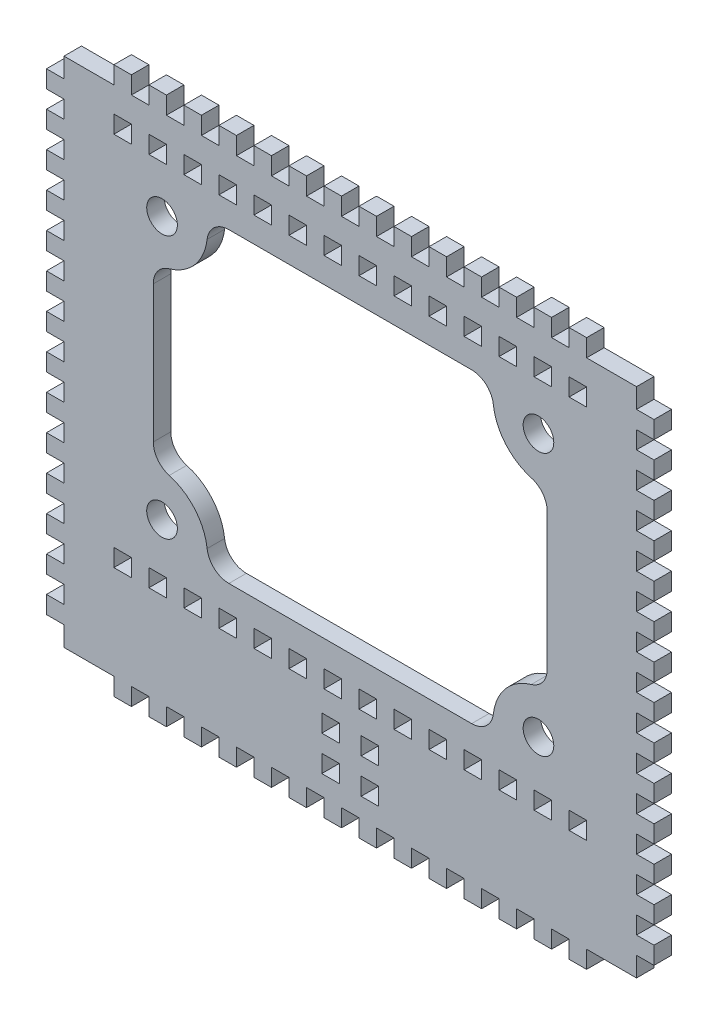
SolidWorks part; units mm, degrees
material "Cedar"
ref_plane "Front Plane" through (0, 0, 0) normal (0, 0, 1) x (1, 0, 0)
ref_plane "Top Plane" through (0, 0, 0) normal (0, 1, 0) x (1, 0, 0)
ref_plane "Right Plane" through (0, 0, 0) normal (1, 0, 0) x (0, 0, -1)
sketch "Sketch1" plane through (0, 0, 0) normal (0, 0, 1) x (1, 0, 0)
  line L0 (0, 0) -> (0, 50) construction
  line L1 (0, 0) -> (-64, 0) construction
  line L2 (-65.4, -66.5) -> (-65.4, -62)
  line L3 (-65.4, 50.5) -> (65.4, 50.5)
  line L4 (-45, -20) -> (-45, 20)
  line L5 (-33, 35) -> (33, 35)
  line L6 (45, -20) -> (45, 20)
  line L7 (65.4, -66.5) -> (65.4, -62)
  line L8 (-65.4, -66.5) -> (65.4, -66.5)
  line L9 (-33, -35) -> (33, -35)
  line L10 (-54.7956, 50.5) -> (-54.7956, -66.5) construction
  line L11 (-65.4, -2) -> (-69.4, -2)
  line L12 (-65.4, -2) -> (-65.4, 2)
  line L13 (-65.4, -6) -> (-69.4, -6)
  line L14 (-69.4, -2) -> (-69.4, -6)
  line L15 (-54.7956, -8) -> (-65.4, -8) construction
  line L16 (-65.4, 6) -> (-69.4, 6)
  line L17 (65.4, -58) -> (65.4, -54)
  line L18 (-65.4, 2) -> (-69.4, 2)
  line L19 (-69.4, 6) -> (-69.4, 2)
  line L20 (-65.4, 14) -> (-69.4, 14)
  line L21 (-65.4, -58) -> (-65.4, -54)
  line L22 (-65.4, 10) -> (-69.4, 10)
  line L23 (-69.4, 14) -> (-69.4, 10)
  line L24 (-65.4, 22) -> (-69.4, 22)
  line L25 (-65.4, 14) -> (-65.4, 18)
  line L26 (-65.4, 18) -> (-69.4, 18)
  line L27 (-69.4, 22) -> (-69.4, 18)
  line L28 (-65.4, 30) -> (-69.4, 30)
  line L29 (-65.4, 22) -> (-65.4, 26)
  line L30 (-65.4, 26) -> (-69.4, 26)
  line L31 (-69.4, 30) -> (-69.4, 26)
  line L32 (-65.4, 38) -> (-69.4, 38)
  line L33 (-65.4, 46) -> (-65.4, 50.5)
  line L34 (-65.4, 34) -> (-69.4, 34)
  line L35 (-69.4, 38) -> (-69.4, 34)
  line L36 (-65.4, 46) -> (-69.4, 46)
  line L37 (-65.4, 30) -> (-65.4, 34)
  line L38 (-65.4, 42) -> (-69.4, 42)
  line L39 (-69.4, 46) -> (-69.4, 42)
  line L40 (-69.4, -62) -> (-69.4, -58)
  line L41 (-65.4, -58) -> (-69.4, -58)
  line L42 (-65.4, -50) -> (-65.4, -46)
  line L43 (-65.4, -62) -> (-69.4, -62)
  line L44 (-69.4, -54) -> (-69.4, -50)
  line L45 (-65.4, -50) -> (-69.4, -50)
  line L46 (-65.4, -42) -> (-65.4, -38)
  line L47 (-65.4, -54) -> (-69.4, -54)
  line L48 (-69.4, -46) -> (-69.4, -42)
  line L49 (-65.4, -42) -> (-69.4, -42)
  line L50 (-65.4, -34) -> (-65.4, -30)
  line L51 (-65.4, -46) -> (-69.4, -46)
  line L52 (-69.4, -38) -> (-69.4, -34)
  line L53 (-65.4, -34) -> (-69.4, -34)
  line L55 (-65.4, -38) -> (-69.4, -38)
  line L56 (-69.4, -30) -> (-69.4, -26)
  line L57 (-65.4, -26) -> (-69.4, -26)
  line L58 (-65.4, -18) -> (-65.4, -14)
  line L59 (-65.4, -30) -> (-69.4, -30)
  line L60 (-69.4, -22) -> (-69.4, -18)
  line L61 (-65.4, -18) -> (-69.4, -18)
  line L62 (-65.4, -10) -> (-65.4, -6)
  line L63 (-65.4, -22) -> (-69.4, -22)
  line L64 (-69.4, -14) -> (-69.4, -10)
  line L65 (-65.4, -10) -> (-69.4, -10)
  line L66 (-65.4, 6) -> (-65.4, 10)
  line L67 (-65.4, -14) -> (-69.4, -14)
  line L68 (65.4, -14) -> (69.4, -14)
  line L69 (65.4, -10) -> (65.4, -6)
  line L70 (65.4, -10) -> (69.4, -10)
  line L71 (69.4, -14) -> (69.4, -10)
  line L72 (65.4, -22) -> (69.4, -22)
  line L73 (65.4, -18) -> (65.4, -14)
  line L74 (65.4, -18) -> (69.4, -18)
  line L75 (69.4, -22) -> (69.4, -18)
  line L76 (65.4, -30) -> (69.4, -30)
  line L77 (65.4, -26) -> (65.4, -22)
  line L78 (65.4, -26) -> (69.4, -26)
  line L79 (69.4, -30) -> (69.4, -26)
  line L80 (65.4, -38) -> (69.4, -38)
  line L81 (65.4, -34) -> (65.4, -30)
  line L82 (65.4, -34) -> (69.4, -34)
  line L83 (69.4, -38) -> (69.4, -34)
  line L84 (65.4, -46) -> (69.4, -46)
  line L85 (65.4, -50) -> (65.4, -46)
  line L86 (65.4, -42) -> (69.4, -42)
  line L87 (69.4, -46) -> (69.4, -42)
  line L88 (65.4, -54) -> (69.4, -54)
  line L89 (65.4, -2) -> (65.4, 2)
  line L90 (65.4, -50) -> (69.4, -50)
  line L91 (69.4, -54) -> (69.4, -50)
  line L92 (65.4, -62) -> (69.4, -62)
  line L93 (65.4, -42) -> (65.4, -38)
  line L94 (65.4, -58) -> (69.4, -58)
  line L95 (69.4, -62) -> (69.4, -58)
  line L96 (69.4, 46) -> (69.4, 42)
  line L97 (65.4, 42) -> (69.4, 42)
  line L98 (65.4, 46) -> (65.4, 50.5)
  line L99 (65.4, 46) -> (69.4, 46)
  line L100 (69.4, 38) -> (69.4, 34)
  line L101 (65.4, 34) -> (69.4, 34)
  line L102 (65.4, 38) -> (65.4, 42)
  line L103 (65.4, 38) -> (69.4, 38)
  line L104 (69.4, 30) -> (69.4, 26)
  line L105 (65.4, 26) -> (69.4, 26)
  line L106 (65.4, 30) -> (65.4, 34)
  line L107 (65.4, 30) -> (69.4, 30)
  line L108 (69.4, 22) -> (69.4, 18)
  line L109 (65.4, 18) -> (69.4, 18)
  line L110 (65.4, 22) -> (65.4, 26)
  line L111 (65.4, 22) -> (69.4, 22)
  line L112 (69.4, 14) -> (69.4, 10)
  line L113 (65.4, 10) -> (69.4, 10)
  line L114 (65.4, 14) -> (65.4, 18)
  line L115 (65.4, 14) -> (69.4, 14)
  line L116 (69.4, 6) -> (69.4, 2)
  line L117 (65.4, 2) -> (69.4, 2)
  line L119 (65.4, 6) -> (69.4, 6)
  line L120 (69.4, -2) -> (69.4, -6)
  line L121 (65.4, -6) -> (69.4, -6)
  line L123 (65.4, -2) -> (69.4, -2)
  line L124 (-65.4, 38) -> (-65.4, 42)
  line L130 (-65.4, -26) -> (-65.4, -22)
  line L131 (65.4, 6) -> (65.4, 10)
  circle A0 centre (-43, 30) radius 3.5
  arc A1 (-45, 20) -> (-33, 35) centre (-44.6174, 31.9939) ccw
  arc A2 (45, -20) -> (33, -35) centre (44.6174, -31.9939) ccw
  circle A3 centre (43, 30) radius 3.5
  circle A4 centre (43, -30) radius 3.5
  circle A5 centre (-43, -30) radius 3.5
  arc A6 (45, 20) -> (33, 35) centre (44.6174, 31.9939) cw
  arc A7 (-45, -20) -> (-33, -35) centre (-44.6174, -31.9939) cw
  point P19 (0, 35)
  point P21 (0, 50.5)
  point P27 (-64, 0)
  point P28 (64, 0)
  point P29 (45, 0)
  point P34 (-45, 0)
  point P94 (-64, -16)
  point P151 (64, -16)
  dimension "D3" = 7
  dimension "D8" = 50.5
  dimension "D7" = 10
  dimension "D9" = 35
  dimension "D10" = 12
  dimension "D11" = 66.5
  dimension "D1" = 10
  dimension "D2" = 130.8
  dimension "D4" = 43
  dimension "D5" = 45
  dimension "D6" = 30
  dimension "D12" = 4
  dimension "D13" = 2
  dimension "D14" = 4
  dimension "D15" = 7
extrude "Boss-Extrude1" add sketch "Sketch1" along normal blind 4
sketch "Sketch3" plane through (0, 0, 4) normal (0, 0, 1) x (1, 0, 0)
  line L0 (0, 0) -> (0, 54.6046) construction
  line L2 (-54, -45) -> (-50, -45)
  line L3 (-54, -45) -> (-54, -41)
  line L4 (-54, -41) -> (-50, -41)
  line L5 (-50, -45) -> (-50, -41)
  line L6 (33, 35) -> (33, 50.5) construction
  line L7 (-65.4, 50.5) -> (65.4, 50.5) construction
  line L8 (42, -45) -> (42, -41)
  line L9 (46, -41) -> (42, -41)
  line L10 (46, -45) -> (46, -41)
  line L11 (-6.5, -50) -> (-2.5, -50)
  line L12 (46, -45) -> (42, -45)
  line L13 (0, -35) -> (0, -66.5) construction
  line L14 (34, -45) -> (34, -41)
  line L15 (0, 0) -> (-26.3378, 0) construction
  line L16 (0, 0) -> (-64, 0) construction
  line L17 (-33, -35) -> (33, -35) construction
  line L18 (-65.4, -66.5) -> (65.4, -66.5) construction
  line L19 (38, -41) -> (34, -41)
  line L20 (38, -45) -> (38, -41)
  line L21 (38, -45) -> (34, -45)
  line L22 (26, -45) -> (26, -41)
  line L23 (30, -41) -> (26, -41)
  line L24 (30, -45) -> (30, -41)
  line L25 (30, -45) -> (26, -45)
  line L26 (18, -45) -> (18, -41)
  line L27 (22, -41) -> (18, -41)
  line L28 (22, -45) -> (22, -41)
  line L29 (22, -45) -> (18, -45)
  line L30 (10, -45) -> (10, -41)
  line L31 (14, -41) -> (10, -41)
  line L32 (14, -45) -> (14, -41)
  line L33 (2, -45) -> (2, -41)
  line L34 (-6.5, -50) -> (-6.5, -54)
  line L35 (6, -41) -> (2, -41)
  line L36 (6, -45) -> (6, -41)
  line L37 (6, -45) -> (2, -45)
  line L38 (-6.5, -54) -> (-2.5, -54)
  line L39 (14, -45) -> (10, -45)
  line L40 (50, -45) -> (50, -41)
  line L41 (54, -41) -> (50, -41)
  line L42 (54, -45) -> (54, -41)
  line L43 (54, -45) -> (50, -45)
  line L44 (33, 42.75) -> (-16.2732, 42.75) construction
  line L45 (-14, 40.75) -> (-10, 40.75)
  line L46 (-6, 40.75) -> (-2, 40.75)
  line L47 (-6, 40.75) -> (-6, 44.75)
  line L48 (-6, 44.75) -> (-2, 44.75)
  line L49 (-2, 40.75) -> (-2, 44.75)
  line L50 (-14, 40.75) -> (-14, 44.75)
  line L51 (-14, 44.75) -> (-10, 44.75)
  line L52 (-10, 40.75) -> (-10, 44.75)
  line L53 (-22, 40.75) -> (-18, 40.75)
  line L54 (-22, 40.75) -> (-22, 44.75)
  line L55 (-22, 44.75) -> (-18, 44.75)
  line L56 (-18, 40.75) -> (-18, 44.75)
  line L57 (-30, 40.75) -> (-26, 40.75)
  line L58 (-30, 40.75) -> (-30, 44.75)
  line L59 (-30, 44.75) -> (-26, 44.75)
  line L60 (-26, 40.75) -> (-26, 44.75)
  line L61 (-38, 40.75) -> (-34, 40.75)
  line L62 (-38, 40.75) -> (-38, 44.75)
  line L63 (-14, -45) -> (-10, -45)
  line L64 (-6, -45) -> (-2, -45)
  line L65 (-6, -45) -> (-6, -41)
  line L66 (-6, -41) -> (-2, -41)
  line L67 (-2, -45) -> (-2, -41)
  line L68 (-14, -45) -> (-14, -41)
  line L69 (-14, -41) -> (-10, -41)
  line L70 (-10, -45) -> (-10, -41)
  line L71 (-22, -45) -> (-18, -45)
  line L72 (-22, -45) -> (-22, -41)
  line L73 (-22, -41) -> (-18, -41)
  line L74 (-18, -45) -> (-18, -41)
  line L75 (-30, -45) -> (-26, -45)
  line L76 (-30, -45) -> (-30, -41)
  line L77 (-30, -41) -> (-26, -41)
  line L78 (-26, -45) -> (-26, -41)
  line L79 (-38, -45) -> (-34, -45)
  line L80 (-38, -45) -> (-38, -41)
  line L81 (-38, -41) -> (-34, -41)
  line L82 (-34, -45) -> (-34, -41)
  line L83 (-46, -45) -> (-42, -45)
  line L84 (-46, -45) -> (-46, -41)
  line L85 (-46, -41) -> (-42, -41)
  line L86 (-42, -45) -> (-42, -41)
  line L87 (-38, 44.75) -> (-34, 44.75)
  line L88 (-34, 40.75) -> (-34, 44.75)
  line L89 (-46, 40.75) -> (-42, 40.75)
  line L90 (-46, 40.75) -> (-46, 44.75)
  line L91 (-46, 44.75) -> (-42, 44.75)
  line L92 (-42, 40.75) -> (-42, 44.75)
  line L93 (-54, 40.75) -> (-50, 40.75)
  line L94 (-54, 40.75) -> (-54, 44.75)
  line L95 (-54, 44.75) -> (-50, 44.75)
  line L96 (-25.103, -50.75) -> (0, -50.75) construction
  line L97 (-50, 40.75) -> (-50, 44.75)
  line L98 (50, 40.75) -> (50, 44.75)
  line L99 (54, 44.75) -> (50, 44.75)
  line L100 (54, 40.75) -> (54, 44.75)
  line L101 (54, 40.75) -> (50, 40.75)
  line L102 (42, 40.75) -> (42, 44.75)
  line L103 (46, 44.75) -> (42, 44.75)
  line L104 (46, 40.75) -> (46, 44.75)
  line L105 (46, 40.75) -> (42, 40.75)
  line L106 (34, 40.75) -> (34, 44.75)
  line L107 (38, 44.75) -> (34, 44.75)
  line L108 (38, 40.75) -> (38, 44.75)
  line L109 (38, 40.75) -> (34, 40.75)
  line L110 (26, 40.75) -> (26, 44.75)
  line L111 (30, 44.75) -> (26, 44.75)
  line L112 (30, 40.75) -> (30, 44.75)
  line L113 (30, 40.75) -> (26, 40.75)
  line L114 (18, 40.75) -> (18, 44.75)
  line L115 (22, 44.75) -> (18, 44.75)
  line L116 (22, 40.75) -> (22, 44.75)
  line L117 (22, 40.75) -> (18, 40.75)
  line L118 (10, 40.75) -> (10, 44.75)
  line L119 (14, 44.75) -> (10, 44.75)
  line L120 (14, 40.75) -> (14, 44.75)
  line L121 (2, 40.75) -> (2, 44.75)
  line L122 (6, 44.75) -> (2, 44.75)
  line L123 (-2.5, -50) -> (-2.5, -54)
  line L124 (6, 40.75) -> (6, 44.75)
  line L125 (6, 40.75) -> (2, 40.75)
  line L126 (2.5, -50) -> (6.5, -50)
  line L127 (14, 40.75) -> (10, 40.75)
  line L128 (2.5, -50) -> (2.5, -54)
  line L129 (2.5, -54) -> (6.5, -54)
  line L130 (6.5, -50) -> (6.5, -54)
  line L131 (-6.5, -58) -> (-2.5, -58)
  line L132 (-6.5, -58) -> (-6.5, -62)
  line L133 (-6.5, -62) -> (-2.5, -62)
  line L134 (-2.5, -58) -> (-2.5, -62)
  line L135 (2.5, -58) -> (6.5, -58)
  line L136 (2.5, -58) -> (2.5, -62)
  line L137 (2.5, -62) -> (6.5, -62)
  line L138 (6.5, -58) -> (6.5, -62)
  dimension "D2" = 6
  dimension "D3" = 2
  dimension "D4" = 2
  dimension "D6" = 4
  dimension "D7" = 2
  dimension "D8" = 5
  dimension "D9" = 4
  dimension "D11" = 4
  dimension "D13" = 2.5
  dimension "D15" = 4
  dimension "D16" = 4
  dimension "D5" = 4
  dimension "D10" = 2.5
  dimension "D12" = 4
  dimension "D19" = 7
extrude "Cut-Extrude2" cut sketch "Sketch3" against normal blind 4
fillet "Fillet1" radius 5 1 edges at (-45, 20, 2)
fillet "Fillet2" radius 5 1 edges at (-33, 35, 2)
fillet "Fillet3" radius 5 1 edges at (33, 35, 2)
fillet "Fillet4" radius 5 1 edges at (45, 20, 2)
fillet "Fillet5" radius 5 1 edges at (33, -35, 2)
fillet "Fillet6" radius 5 1 edges at (45, -20, 2)
fillet "Fillet7" radius 5 1 edges at (-45, -20, 2)
fillet "Fillet8" radius 5 1 edges at (-33, -35, 2)
sketch "Sketch5" plane through (0, 0, 4) normal (0, 0, 1) x (1, 0, 0)
  line L1 (-65.4, 50.5) -> (65.4, 50.5) construction
  line L2 (-2, 50.5) -> (-6, 50.5)
  line L3 (-2, 50.5) -> (-2, 54.5)
  line L4 (-2, 54.5) -> (-6, 54.5)
  line L6 (0, 50.5) -> (0, 35) construction
  line L8 (-65.4, -8) -> (-54.7956, -8) construction
  line L10 (-6, 50.5) -> (-6, 54.5)
  line L11 (-10, 50.5) -> (-14, 50.5)
  line L12 (-10, 50.5) -> (-10, 54.5)
  line L13 (-10, 54.5) -> (-14, 54.5)
  line L14 (-14, 50.5) -> (-14, 54.5)
  line L15 (-18, 50.5) -> (-22, 50.5)
  line L16 (-18, 50.5) -> (-18, 54.5)
  line L17 (-18, 54.5) -> (-22, 54.5)
  line L18 (-22, 50.5) -> (-22, 54.5)
  line L19 (-26, 50.5) -> (-30, 50.5)
  line L20 (-26, 50.5) -> (-26, 54.5)
  line L21 (-26, 54.5) -> (-30, 54.5)
  line L22 (-30, 50.5) -> (-30, 54.5)
  line L23 (-34, 50.5) -> (-38, 50.5)
  line L24 (-34, 50.5) -> (-34, 54.5)
  line L25 (-34, 54.5) -> (-38, 54.5)
  line L26 (-38, 50.5) -> (-38, 54.5)
  line L27 (-42, 50.5) -> (-46, 50.5)
  line L28 (-42, 50.5) -> (-42, 54.5)
  line L29 (-42, 54.5) -> (-46, 54.5)
  line L30 (-46, 50.5) -> (-46, 54.5)
  line L31 (-50, 50.5) -> (-54, 50.5)
  line L32 (-50, 50.5) -> (-50, 54.5)
  line L33 (-50, 54.5) -> (-54, 54.5)
  line L34 (-54, 50.5) -> (-54, 54.5)
  line L43 (54, 50.5) -> (54, 54.5)
  line L44 (50, 54.5) -> (54, 54.5)
  line L45 (50, 50.5) -> (50, 54.5)
  line L46 (50, 50.5) -> (54, 50.5)
  line L47 (46, 50.5) -> (46, 54.5)
  line L48 (42, 54.5) -> (46, 54.5)
  line L49 (42, 50.5) -> (42, 54.5)
  line L50 (42, 50.5) -> (46, 50.5)
  line L51 (38, 50.5) -> (38, 54.5)
  line L52 (34, 54.5) -> (38, 54.5)
  line L53 (34, 50.5) -> (34, 54.5)
  line L54 (34, 50.5) -> (38, 50.5)
  line L55 (30, 50.5) -> (30, 54.5)
  line L56 (26, 54.5) -> (30, 54.5)
  line L57 (26, 50.5) -> (26, 54.5)
  line L58 (26, 50.5) -> (30, 50.5)
  line L59 (22, 50.5) -> (22, 54.5)
  line L60 (18, 54.5) -> (22, 54.5)
  line L61 (18, 50.5) -> (18, 54.5)
  line L62 (18, 50.5) -> (22, 50.5)
  line L63 (14, 50.5) -> (14, 54.5)
  line L64 (10, 54.5) -> (14, 54.5)
  line L65 (10, 50.5) -> (10, 54.5)
  line L66 (10, 50.5) -> (14, 50.5)
  line L67 (6, 50.5) -> (6, 54.5)
  line L68 (2, 54.5) -> (6, 54.5)
  line L69 (2, 50.5) -> (2, 54.5)
  line L70 (2, 50.5) -> (6, 50.5)
  line L71 (2, -66.5) -> (6, -66.5)
  line L72 (2, -66.5) -> (2, -70.5)
  line L73 (2, -70.5) -> (6, -70.5)
  line L74 (6, -66.5) -> (6, -70.5)
  line L75 (10, -66.5) -> (14, -66.5)
  line L76 (10, -66.5) -> (10, -70.5)
  line L77 (10, -70.5) -> (14, -70.5)
  line L78 (14, -66.5) -> (14, -70.5)
  line L79 (18, -66.5) -> (22, -66.5)
  line L80 (18, -66.5) -> (18, -70.5)
  line L81 (18, -70.5) -> (22, -70.5)
  line L82 (22, -66.5) -> (22, -70.5)
  line L83 (26, -66.5) -> (30, -66.5)
  line L84 (26, -66.5) -> (26, -70.5)
  line L85 (26, -70.5) -> (30, -70.5)
  line L86 (30, -66.5) -> (30, -70.5)
  line L87 (34, -66.5) -> (38, -66.5)
  line L88 (34, -66.5) -> (34, -70.5)
  line L89 (34, -70.5) -> (38, -70.5)
  line L90 (38, -66.5) -> (38, -70.5)
  line L91 (42, -66.5) -> (46, -66.5)
  line L92 (42, -66.5) -> (42, -70.5)
  line L93 (42, -70.5) -> (46, -70.5)
  line L94 (46, -66.5) -> (46, -70.5)
  line L95 (50, -66.5) -> (54, -66.5)
  line L96 (50, -66.5) -> (50, -70.5)
  line L97 (50, -70.5) -> (54, -70.5)
  line L98 (54, -66.5) -> (54, -70.5)
  line L107 (-54, -66.5) -> (-54, -70.5)
  line L108 (-50, -70.5) -> (-54, -70.5)
  line L109 (-50, -66.5) -> (-50, -70.5)
  line L110 (-50, -66.5) -> (-54, -66.5)
  line L111 (-46, -66.5) -> (-46, -70.5)
  line L112 (-42, -70.5) -> (-46, -70.5)
  line L113 (-42, -66.5) -> (-42, -70.5)
  line L114 (-42, -66.5) -> (-46, -66.5)
  line L115 (-38, -66.5) -> (-38, -70.5)
  line L116 (-34, -70.5) -> (-38, -70.5)
  line L117 (-34, -66.5) -> (-34, -70.5)
  line L118 (-34, -66.5) -> (-38, -66.5)
  line L119 (-30, -66.5) -> (-30, -70.5)
  line L120 (-26, -70.5) -> (-30, -70.5)
  line L121 (-26, -66.5) -> (-26, -70.5)
  line L122 (-26, -66.5) -> (-30, -66.5)
  line L123 (-22, -66.5) -> (-22, -70.5)
  line L124 (-18, -70.5) -> (-22, -70.5)
  line L125 (-18, -66.5) -> (-18, -70.5)
  line L126 (-18, -66.5) -> (-22, -66.5)
  line L127 (-14, -66.5) -> (-14, -70.5)
  line L128 (-10, -70.5) -> (-14, -70.5)
  line L129 (-10, -66.5) -> (-10, -70.5)
  line L130 (-10, -66.5) -> (-14, -66.5)
  line L131 (-6, -66.5) -> (-6, -70.5)
  line L132 (-2, -70.5) -> (-6, -70.5)
  line L133 (-2, -66.5) -> (-2, -70.5)
  line L134 (-2, -66.5) -> (-6, -66.5)
  dimension "D1" = 2
  dimension "D2" = 4
  dimension "D3" = 4
  dimension "D4" = 7
extrude "Boss-Extrude2" add sketch "Sketch5" against normal blind 4
